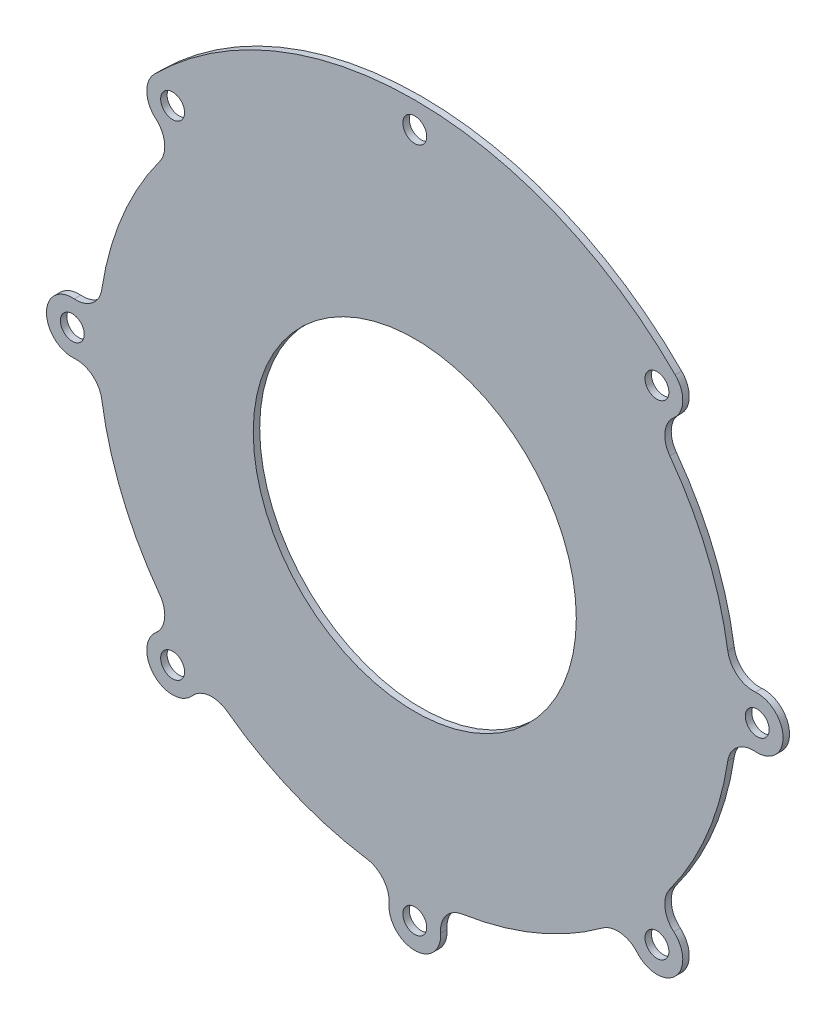
SolidWorks part; units mm, degrees
ref_plane "Ön Düzlem" through (0, 0, 0) normal (0, 0, 1) x (1, 0, 0)
ref_plane "Üst Düzlem" through (0, 0, 0) normal (0, 1, 0) x (1, 0, 0)
ref_plane "Sağ Düzlem" through (0, 0, 0) normal (1, 0, 0) x (0, 0, -1)
sketch "NPTH" plane through (0, 0, 0) normal (0, 0, 1) x (1, 0, 0)
  circle A0 centre (0, 0) radius 25
  arc A1 (-39.4685, 29.0385) -> (-48.4418, 7.3751) centre (0, 0) ccw
  arc A2 (40.3051, 40.3051) -> (-40.3051, 40.3051) centre (0, 0) ccw
  circle A3 centre (0, -53) radius 1.85
  circle A4 centre (0, 0) radius 53 construction
  arc A5 (-3.9886, -52.6981) -> (3.9886, -52.6981) centre (0, -53) ccw
  arc A6 (7.3751, -48.4418) -> (4.0028, -52.8486) centre (7.9772, -52.3962) ccw
  arc A7 (-4.0028, -52.8486) -> (-7.3751, -48.4418) centre (-7.9772, -52.3962) ccw
  arc A8 (-29.0385, -39.4685) -> (-34.5392, -40.2001) centre (-31.409, -42.6904) ccw
  circle A9 centre (-37.4767, -37.4767) radius 1.85
  arc A10 (-40.0836, -34.4428) -> (-34.4428, -40.0836) centre (-37.4767, -37.4767) ccw
  arc A11 (-40.2001, -34.5392) -> (-39.4685, -29.0385) centre (-42.6904, -31.409) ccw
  arc A12 (-48.4418, -7.3751) -> (-52.8486, -4.0028) centre (-52.3962, -7.9772) ccw
  circle A13 centre (-53, 0) radius 1.85
  arc A14 (-52.6981, 3.9886) -> (-52.6981, -3.9886) centre (-53, 0) ccw
  arc A15 (-52.8486, 4.0028) -> (-48.4418, 7.3751) centre (-52.3962, 7.9772) ccw
  arc A16 (-39.4685, 29.0385) -> (-40.2001, 34.5392) centre (-42.6904, 31.409) ccw
  circle A17 centre (-37.4767, 37.4767) radius 1.85
  arc A18 (-40.3051, 40.3051) -> (-40.0836, 34.4428) centre (-37.4767, 37.4767) ccw
  circle A21 centre (0, 53) radius 1.85
  circle A25 centre (37.4767, 37.4767) radius 1.85
  arc A26 (40.0836, 34.4428) -> (40.3051, 40.3051) centre (37.4767, 37.4767) ccw
  arc A27 (40.2001, 34.5392) -> (39.4685, 29.0385) centre (42.6904, 31.409) ccw
  arc A28 (48.4418, 7.3751) -> (52.8486, 4.0028) centre (52.3962, 7.9772) ccw
  circle A29 centre (53, 0) radius 1.85
  arc A30 (52.6981, -3.9886) -> (52.6981, 3.9886) centre (53, 0) ccw
  arc A31 (52.8486, -4.0028) -> (48.4418, -7.3751) centre (52.3962, -7.9772) ccw
  arc A32 (39.4685, -29.0385) -> (40.2001, -34.5392) centre (42.6904, -31.409) ccw
  circle A33 centre (37.4767, -37.4767) radius 1.85
  arc A34 (34.4428, -40.0836) -> (40.0836, -34.4428) centre (37.4767, -37.4767) ccw
  arc A35 (34.5392, -40.2001) -> (29.0385, -39.4685) centre (31.409, -42.6904) ccw
  arc A36 (7.3751, -48.4418) -> (29.0385, -39.4685) centre (0, 0) ccw
  arc A37 (39.4685, -29.0385) -> (48.4418, -7.3751) centre (0, 0) ccw
  arc A38 (33.7795, 45.9124) -> (28.0999, 44.9377) centre (31.409, 42.6904) ccw [skipped]
  circle A39 centre (0, 53) radius 4 [skipped]
  circle A40 centre (7.9772, 52.3962) radius 4 [skipped]
  circle A41 centre (-7.9772, 52.3962) radius 4 [skipped]
  circle A42 centre (-31.409, 42.6904) radius 4 [skipped]
  arc A43 (-29.0385, -39.4685) -> (-7.3751, -48.4418) centre (0, 0) ccw
  arc A44 (48.4418, 7.3751) -> (39.4685, 29.0385) centre (0, 0) ccw
  arc A45 (-48.4418, -7.3751) -> (-39.4685, -29.0385) centre (0, 0) ccw
  point P72 (0, 0)
  dimension "D1" = 50
  dimension "D2" = 98
  dimension "D3" = 114
  dimension "D4" = 3.7
  dimension "D5" = 106
  dimension "D6" = 8
  dimension "D7" = 8
extrude "Boss-Extrude1" add sketch "NPTH" along normal blind 1 contours A12 A45 A11 A10 A8 A43 A7 A5 A6 A36 A35 A34 A32 A37 A31 A30 A28 A44 A27 A26 A2 A18 A16 A1 A15 A14 A0 A3 A9 A13 A17 A21 A25 A29 A33
